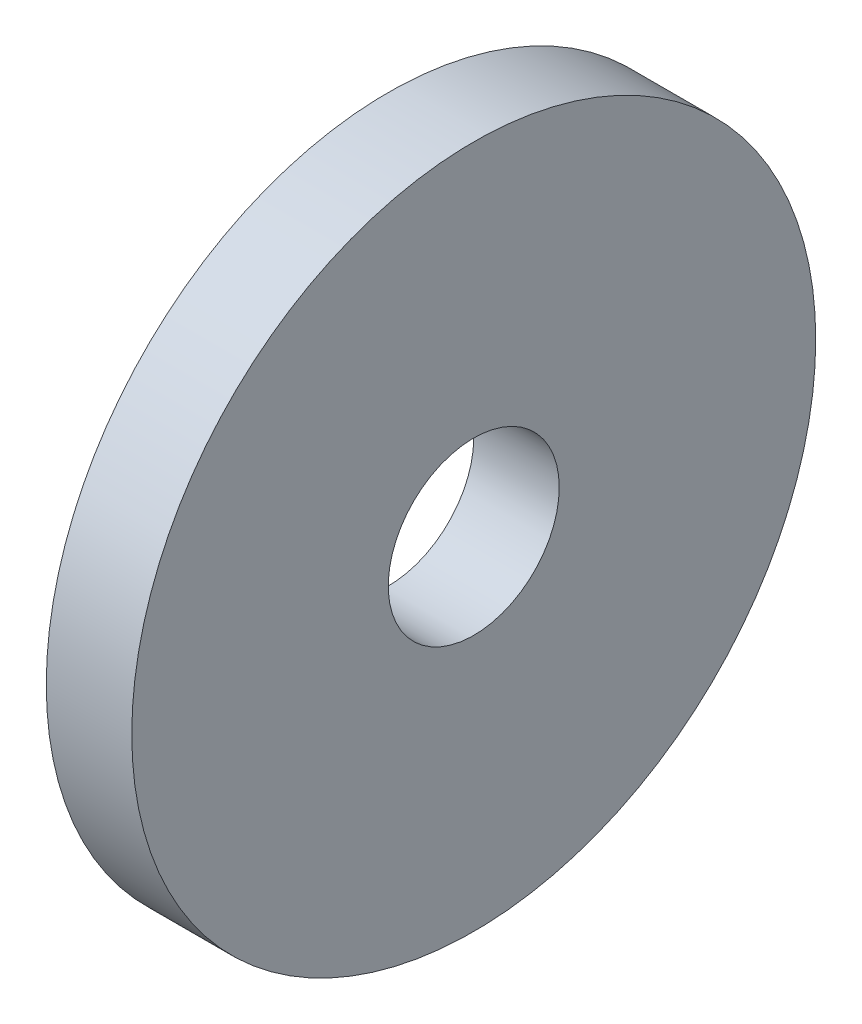
SolidWorks part; units mm, degrees
material "Acrylic (Medium-high impact)"
ref_plane "Front Plane" through (0, 0, 0) normal (0, 0, 1) x (1, 0, 0)
ref_plane "Top Plane" through (0, 0, 0) normal (0, 1, 0) x (1, 0, 0)
ref_plane "Right Plane" through (0, 0, 0) normal (1, 0, 0) x (0, 0, -1)
sketch "Sketch1" plane through (0, 0, 0) normal (1, 0, 0) x (0, 0, -1)
  circle A0 centre (0, 0) radius 12
  dimension "D1" = 24
extrude "Boss-Extrude1" add sketch "Sketch1" along normal blind 3
sketch "Sketch2" plane through (3, 0, 0) normal (1, 0, 0) x (0, 0, -1)
  circle A0 centre (0, 0) radius 3
  dimension "D1" = 6
extrude "Cut-Extrude1" cut sketch "Sketch2" against normal through all and the other way through all
